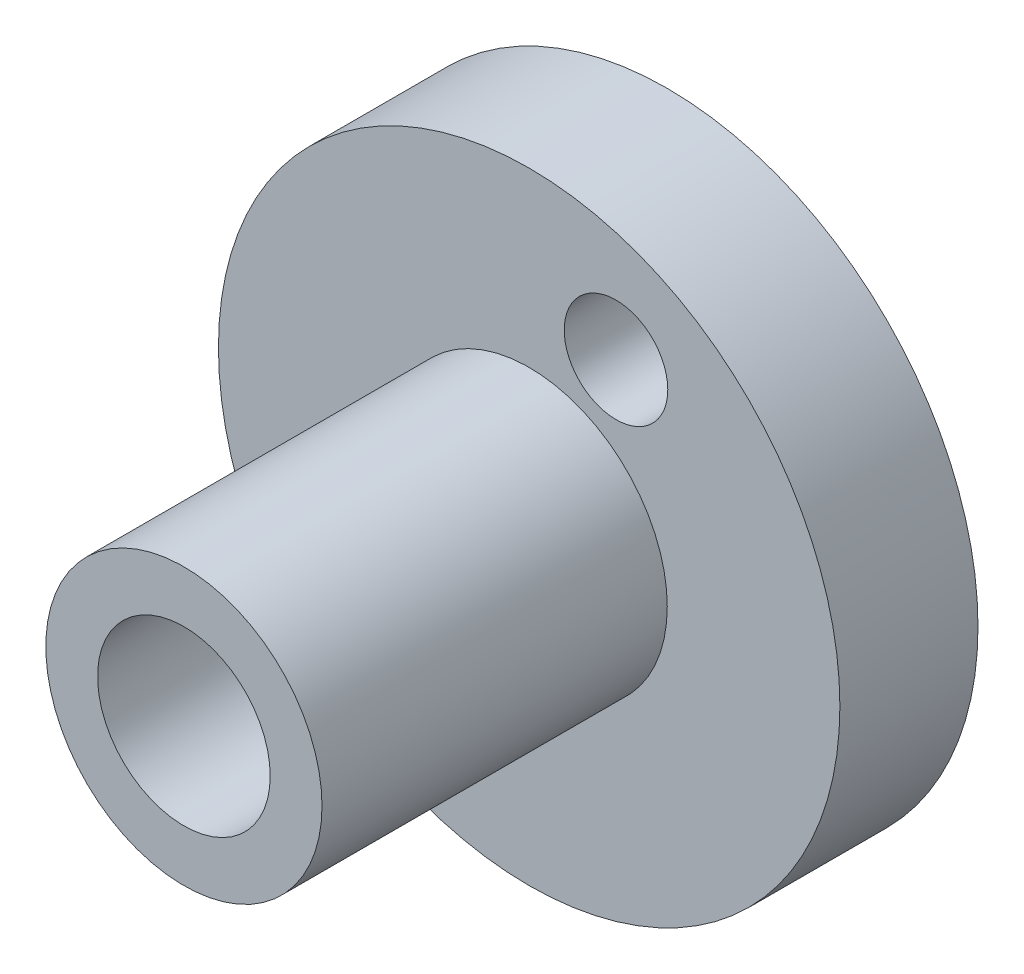
SolidWorks part; units mm, degrees
ref_plane "Front" through (0, 0, 0) normal (0, 0, 1) x (1, 0, 0)
ref_plane "Top" through (0, 0, 0) normal (0, 1, 0) x (1, 0, 0)
ref_plane "Right" through (0, 0, 0) normal (1, 0, 0) x (0, 0, -1)
other "Configuration Table"
sketch "Эскиз1" plane through (0, 0, 0) normal (0, 0, 1) x (1, 0, 0)
  circle A0 centre (0, 0) radius 18
  circle A1 centre (0, 0) radius 5
extrude "Бобышка-Вытянуть1" add sketch "Эскиз1" along normal blind 8
sketch "Эскиз2" plane through (0, 0, 8) normal (0, 0, 1) x (1, 0, 0)
  circle A0 centre (0, 0) radius 5
  circle A1 centre (0, 0) radius 8
  circle A2 centre (0, 0) radius 5 construction
extrude "Бобышка-Вытянуть2" add sketch "Эскиз2" along normal blind 20
sketch "Эскиз3" plane through (0, 0, 0) normal (0, 0, -1) x (-1, 0, 0)
  circle A0 centre (5.0295, -10.8951) radius 3
  dimension "D2" = 6
  dimension "D1" = 12
extrude "Вырез-Вытянуть1" cut sketch "Эскиз3" against normal blind 20
pattern_circular "Круговой массив1" count 2 over 360 about axis through (0, 0, 0) along (0, 0, 1) of "Вырез-Вытянуть1"
